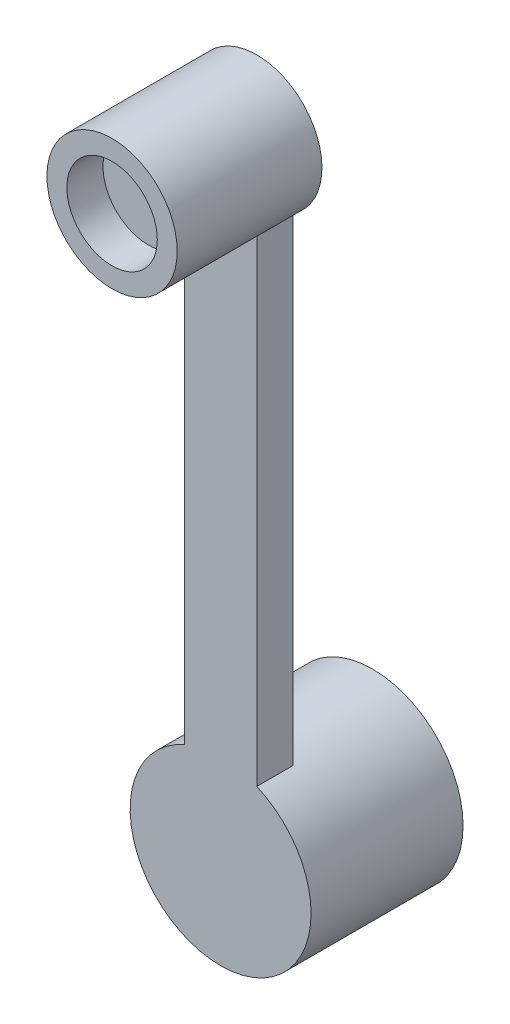
SolidWorks part; units mm, degrees
material "普通碳钢"
ref_plane "前视基准面" through (0, 0, 0) normal (0, 0, 1) x (1, 0, 0)
ref_plane "上视基准面" through (0, 0, 0) normal (0, 1, 0) x (1, 0, 0)
ref_plane "右视基准面" through (0, 0, 0) normal (1, 0, 0) x (0, 0, -1)
sketch "草图1" plane through (0, 0, 0) normal (0, 0, 1) x (1, 0, 0)
  line L0 (0, 0) -> (0, 17) construction
  line L1 (-1, 0) -> (-1, 17)
  line L2 (1, 0) -> (1, 17)
  arc A0 (-1, 0) -> (1, 0) centre (0, 0) ccw
  arc A1 (1, 17) -> (-1, 17) centre (0, 17) ccw
  point P3 (0, 8.5)
  dimension "D1" = 2
  dimension "D2" = 17
extrude "凸台-拉伸1" add sketch "草图1" along normal blind 1
sketch "草图2" plane through (0, 0, 0) normal (0, 0, 1) x (1, 0, 0)
  circle A0 centre (0, 17) radius 1.8
  dimension "D1" = 3.6
extrude "凸台-拉伸2" add sketch "草图2" along normal blind 4
sketch "草图3" plane through (0, 0, 4) normal (0, 0, 1) x (1, 0, 0)
  circle A0 centre (0, 17) radius 1.25
  dimension "D1" = 2.5
extrude "切除-拉伸1" cut sketch "草图3" against normal blind 1
sketch "草图4" plane through (0, 0, 1) normal (0, 0, 1) x (1, 0, 0)
  circle A0 centre (0, 0) radius 2.5
  dimension "D1" = 5
extrude "凸台-拉伸3" add sketch "草图4" against normal blind 4.2
sketch "草图5" plane through (0, 0, -3.2) normal (0, 0, -1) x (-1, 0, 0)
  circle A0 centre (0, 0) radius 1.9
  dimension "D1" = 3.8
extrude "切除-拉伸2" cut sketch "草图5" against normal blind 4
